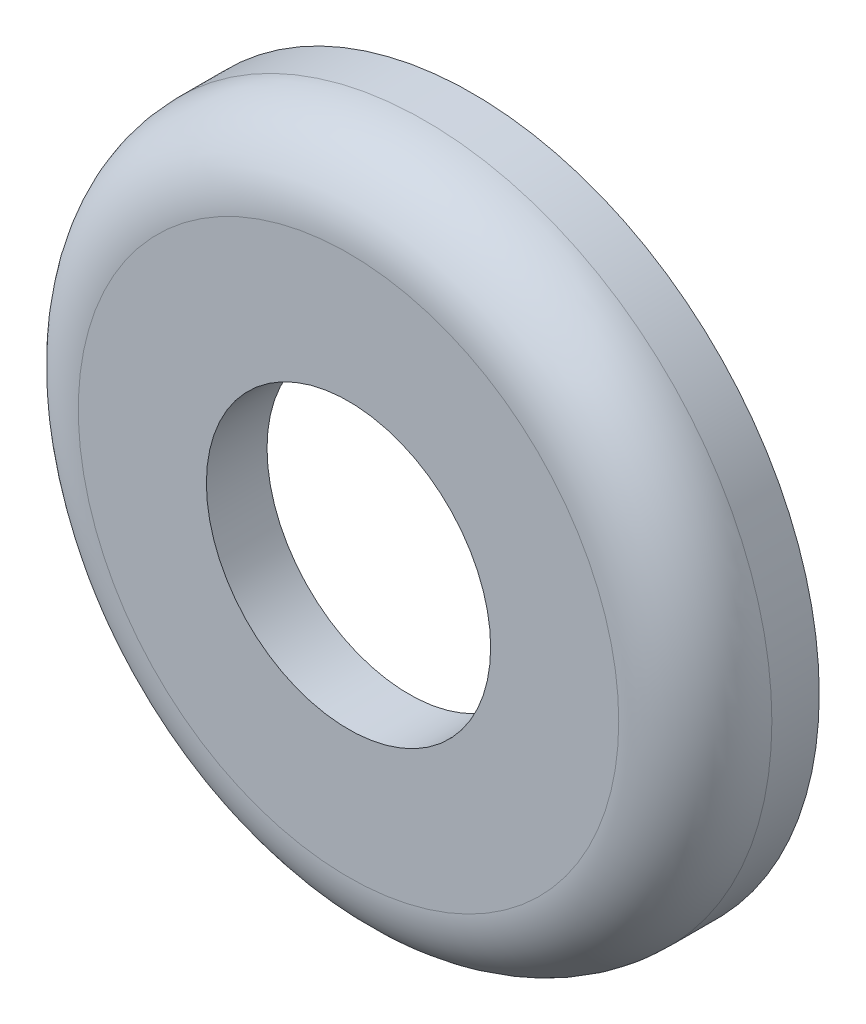
SolidWorks part; units mm, degrees
ref_plane "Front Plane" through (0, 0, 0) normal (0, 0, 1) x (1, 0, 0)
ref_plane "Top Plane" through (0, 0, 0) normal (0, 1, 0) x (1, 0, 0)
ref_plane "Right Plane" through (0, 0, 0) normal (1, 0, 0) x (0, 0, -1)
sketch "Sketch1" plane through (0, 0, 0) normal (0, 1, 0) x (1, 0, 0)
  line L0 (0, 0) -> (0, 5.3831)
  line L1 (4.7625, 2.032) -> (4.7625, 0)
  line L2 (4.7625, 0) -> (9.0551, 0)
  line L3 (11.6205, 2.5654) -> (11.6205, 4.1529)
  line L4 (11.6205, 4.1529) -> (10.033, 4.1529)
  line L5 (10.033, 4.1529) -> (9.4258, 2.305)
  line L6 (4.7625, 2.032) -> (9.0488, 2.032)
  arc A0 (9.0551, 0) -> (11.6205, 2.5654) centre (9.0551, 2.5654) ccw
  arc A1 (9.0488, 2.032) -> (9.4258, 2.305) centre (9.0488, 2.4289) ccw
  dimension "D1" = 4.7625
  dimension "D8" = 9.0488
  dimension "D6" = 0.3969
  dimension "D2" = 2.032
  dimension "D3" = 11.6205
  dimension "D4" = 4.1529
  dimension "D5" = 1.5875
  dimension "D7" = 1.5875
revolve "Revolve1" add sketch "Sketch1" angle 360 about L0
